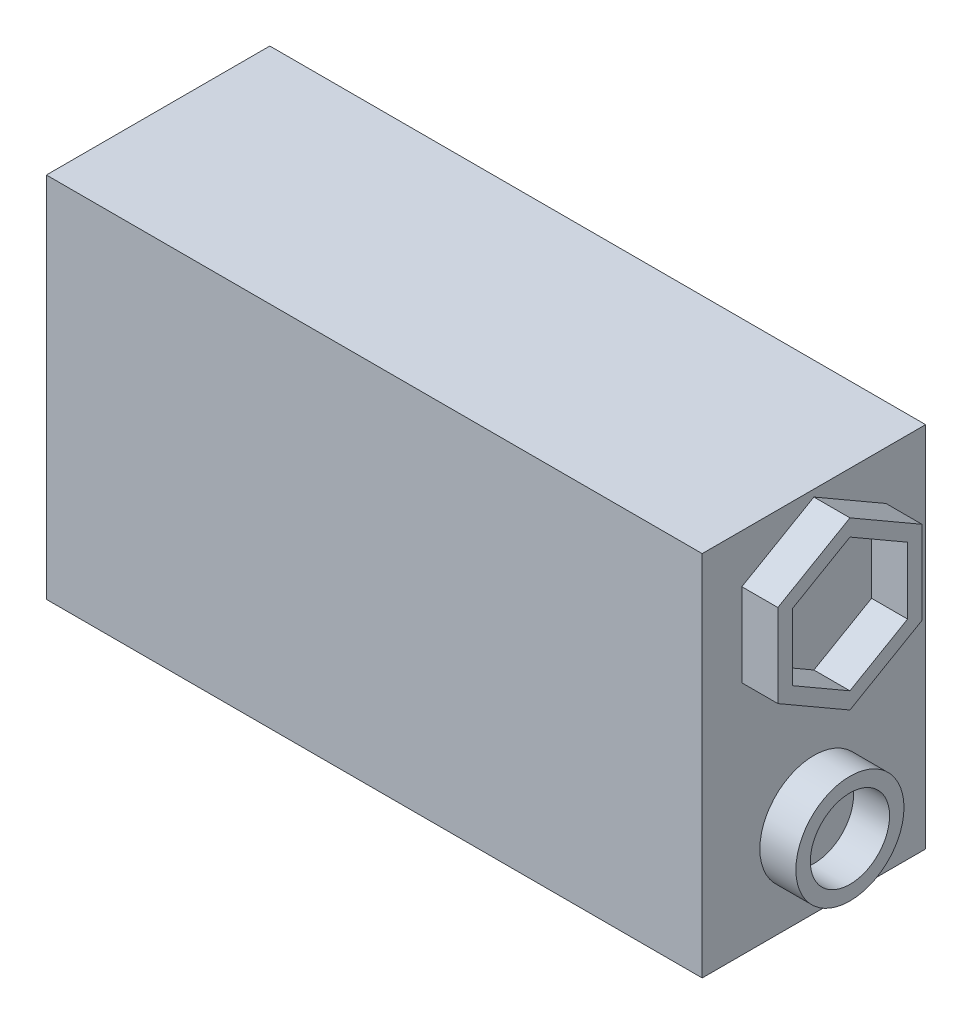
SolidWorks part; units mm, degrees
ref_plane "Alzado" through (0, 0, 0) normal (0, 0, 1) x (1, 0, 0)
ref_plane "Planta" through (0, 0, 0) normal (0, 1, 0) x (1, 0, 0)
ref_plane "Vista lateral" through (0, 0, 0) normal (1, 0, 0) x (0, 0, -1)
sketch "Croquis1" plane through (0, 0, 0) normal (0, 0, 1) x (1, 0, 0)
  line L1 (-22.75, -12.75) -> (22.75, -12.75)
  line L2 (-22.75, -12.75) -> (-22.75, 12.75)
  line L3 (-22.75, 12.75) -> (22.75, 12.75)
  line L4 (22.75, -12.75) -> (22.75, 12.75)
  line L5 (-22.75, -12.75) -> (22.75, 12.75) construction
  line L6 (-22.75, 12.75) -> (22.75, -12.75) construction
  point P0 (0, 0)
  dimension "D1" = 45.5
  dimension "D2" = 25.5
extrude "Saliente-Extruir1" add sketch "Croquis1" along normal mid plane 15.5
sketch "Croquis2" plane through (22.75, 0, 0) normal (1, 0, 0) x (0, 0, -1)
  line L1 (0, 11.1188) -> (-4, 8.8094)
  line L2 (-4, 8.8094) -> (-4, 4.1906)
  line L3 (-4, 4.1906) -> (0, 1.8812)
  line L4 (0, 1.8812) -> (4, 4.1906)
  line L5 (4, 4.1906) -> (4, 8.8094)
  line L6 (4, 8.8094) -> (0, 11.1188)
  circle A0 centre (0, 6.5) radius 4 construction
  circle A1 centre (0, -7) radius 2.75
  point P10 (0, 0)
  dimension "D2" = 5.5
  dimension "D1" = 8
  dimension "D3" = 6.5
  dimension "D4" = 7
extrude "Extruir-Lámina1" add sketch "Croquis2" along normal blind 2.5 thin
